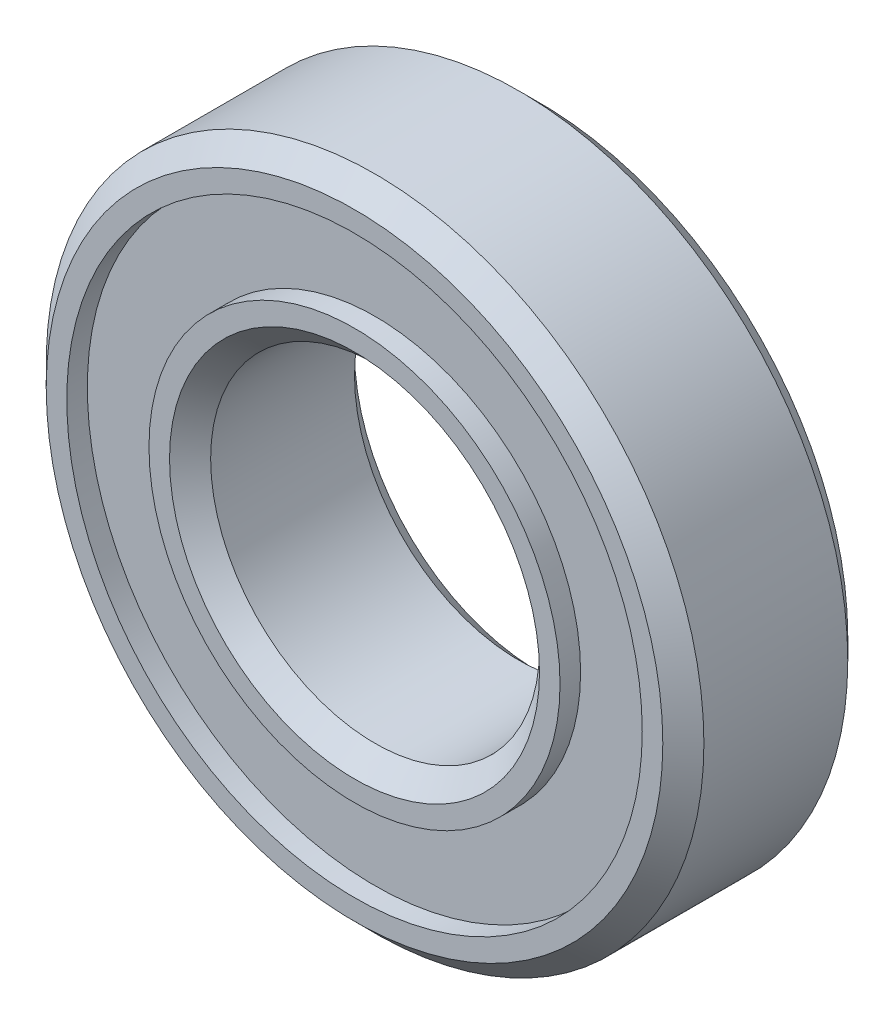
SolidWorks part; units mm, degrees
material "Cast Stainless Steel"
ref_plane "Front Plane" through (0, 0, 0) normal (0, 0, 1) x (1, 0, 0)
ref_plane "Top Plane" through (0, 0, 0) normal (0, 1, 0) x (1, 0, 0)
ref_plane "Right Plane" through (0, 0, 0) normal (1, 0, 0) x (0, 0, -1)
sketch "Sketch1" plane through (0, 0, 0) normal (0, 0, 1) x (1, 0, 0)
  circle A0 centre (0, 0) radius 4
  circle A1 centre (0, 0) radius 8
  dimension "D1" = 8
  dimension "D2" = 16
extrude "Boss-Extrude1" add sketch "Sketch1" along normal blind 4.5
chamfer "Chamfer1" distance 0.5 angle 45 4 edges at (4, 0, 0) (8, 0, 0) (8, 0, 4.5) (4, 0, 4.5)
sketch "Sketch2" plane through (0, 0, 0) normal (0, 0, 1) x (1, 0, 0)
  circle A0 centre (0, 0) radius 5
  circle A1 centre (0, 0) radius 4.5 construction
  circle A2 centre (0, 0) radius 7
  circle A3 centre (0, 0) radius 7.5 construction
  dimension "D1" = 0.5
  dimension "D2" = 0.5
extrude "Cut-Extrude1" cut sketch "Sketch2" along normal blind 0.5
sketch "Sketch3" plane through (0, 0, 4.5) normal (0, 0, 1) x (1, 0, 0)
  circle A0 centre (0, 0) radius 5 construction
  circle A1 centre (0, 0) radius 7 construction
  circle A2 centre (0, 0) radius 5
  circle A3 centre (0, 0) radius 7
extrude "Cut-Extrude2" cut sketch "Sketch3" against normal blind 0.5
